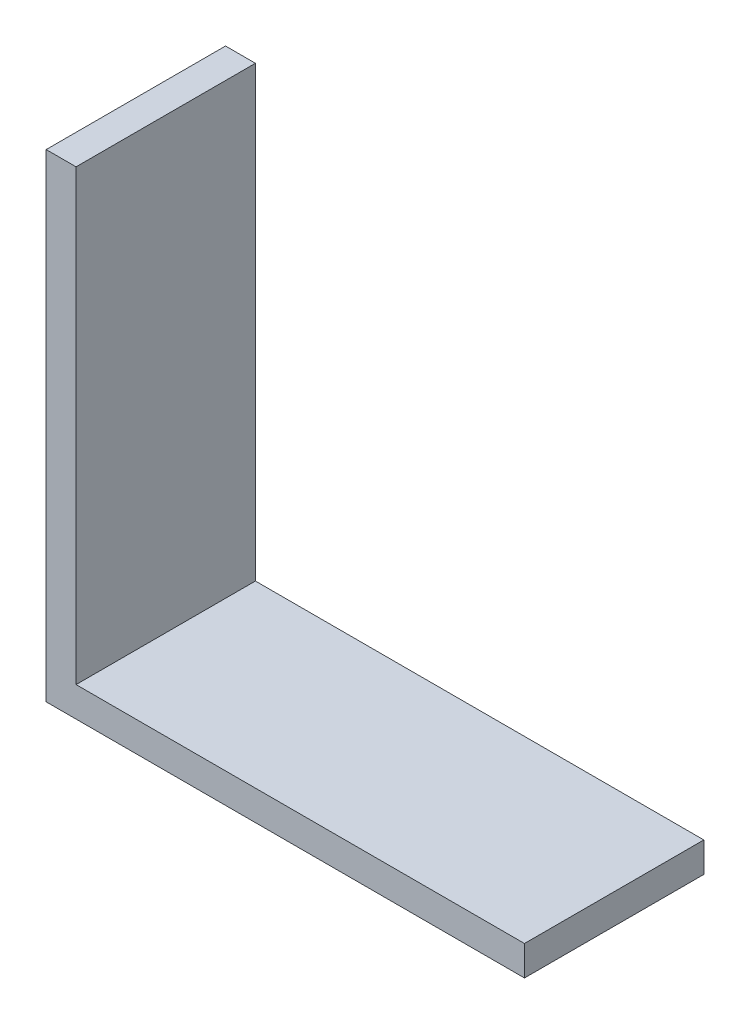
SolidWorks part; units mm, degrees
material "6063-T6"
ref_plane "Front Plane" through (0, 0, 0) normal (0, 0, 1) x (1, 0, 0)
ref_plane "Top Plane" through (0, 0, 0) normal (0, 1, 0) x (1, 0, 0)
ref_plane "Right Plane" through (0, 0, 0) normal (1, 0, 0) x (0, 0, -1)
sketch "Sketch1" plane through (0, 0, 0) normal (0, 0, 1) x (1, 0, 0)
  line L0 (0, 0) -> (0, 50.8)
  line L1 (0, 50.8) -> (3.175, 50.8)
  line L2 (3.175, 50.8) -> (3.175, 3.175)
  line L3 (3.175, 3.175) -> (50.8, 3.175)
  line L4 (50.8, 3.175) -> (50.8, 0)
  line L5 (50.8, 0) -> (0, 0)
  dimension "D1" = 50.8
  dimension "D2" = 3.175
extrude "Boss-Extrude1" add sketch "Sketch1" along normal mid plane 19.05
